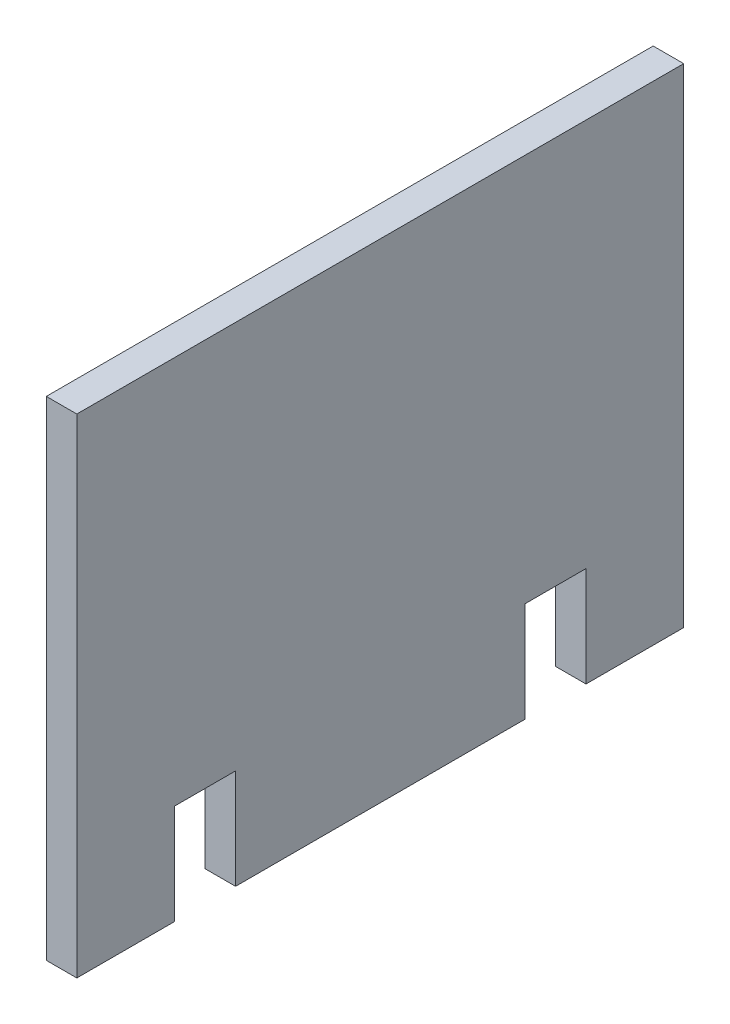
SolidWorks part; units mm, degrees
ref_plane "Front Plane" through (0, 0, 0) normal (0, 0, 1) x (1, 0, 0)
ref_plane "Top Plane" through (0, 0, 0) normal (0, 1, 0) x (1, 0, 0)
ref_plane "Right Plane" through (0, 0, 0) normal (1, 0, 0) x (0, 0, -1)
sketch "Sketch1" plane through (0, 0, 0) normal (1, 0, 0) x (0, 0, -1)
  line L1 (0, 0) -> (63.12, 0)
  line L2 (0, 0) -> (0, 50.8)
  line L3 (0, 50.8) -> (63.12, 50.8)
  line L4 (63.12, 0) -> (63.12, 50.8)
  dimension "D1" = 50.8
  dimension "D2" = 63.12
extrude "Boss-Extrude1" add sketch "Sketch1" along normal blind 3.175
sketch "Sketch2" plane through (3.175, 0, 0) normal (1, 0, 0) x (0, 0, -1)
  line L0 (0, 0) -> (63.12, 0) construction
  line L1 (10.16, 0) -> (16.51, 0)
  line L2 (10.16, 0) -> (10.16, 10.4)
  line L3 (10.16, 10.4) -> (16.51, 10.4)
  line L4 (16.51, 0) -> (16.51, 10.4)
  line L5 (0, 50.8) -> (0, 0) construction
  line L6 (31.56, 50.8) -> (31.56, 0) construction
  line L7 (63.12, 50.8) -> (0, 50.8) construction
  line L8 (52.96, 10.4) -> (46.61, 10.4)
  line L9 (46.61, 0) -> (46.61, 10.4)
  line L10 (52.96, 0) -> (46.61, 0)
  line L11 (52.96, 0) -> (52.96, 10.4)
  dimension "D1" = 10.16
  dimension "D2" = 6.35
  dimension "D3" = 10.4
extrude "Cut-Extrude1" cut sketch "Sketch2" against normal through all
